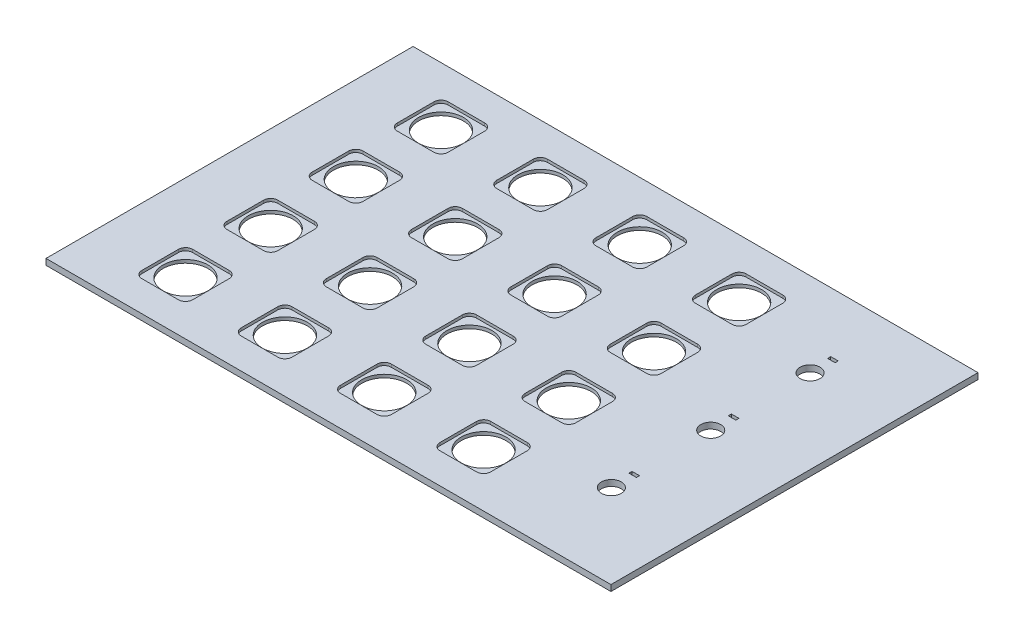
SolidWorks part; units mm, degrees
ref_plane "Front Plane" through (0, 0, 0) normal (0, 0, 1) x (1, 0, 0)
ref_plane "Top Plane" through (0, 0, 0) normal (0, 1, 0) x (1, 0, 0)
ref_plane "Right Plane" through (0, 0, 0) normal (1, 0, 0) x (0, 0, -1)
sketch "Sketch1" plane through (0, 0, 0) normal (0, 1, 0) x (1, 0, 0)
  line L0 (-70, 86.9805) -> (-70, -106.8016) construction
  line L1 (99.5, 64.65) -> (-99.5, 64.65)
  line L2 (99.5, 64.65) -> (99.5, -64.65)
  line L3 (99.5, -64.65) -> (-99.5, -64.65)
  line L4 (-99.5, 64.65) -> (-99.5, -64.65)
  line L5 (99.5, 64.65) -> (-99.5, -64.65) construction
  line L6 (99.5, -64.65) -> (-99.5, 64.65) construction
  line L7 (0, 64.65) -> (0, -64.65) construction
  line L8 (-99.5, 0) -> (99.5, 0) construction
  line L9 (-70, 45) -> (-35, 45) construction
  line L10 (60.6732, 35) -> (77.1303, 35) construction
  line L11 (68.675, 43.6) -> (71.325, 43.6)
  line L12 (68.675, 43.6) -> (68.675, 42.5)
  line L13 (68.675, 42.5) -> (71.325, 42.5)
  line L14 (71.325, 43.6) -> (71.325, 42.5)
  line L15 (68.675, 43.6) -> (71.325, 42.5) construction
  line L16 (68.675, 42.5) -> (71.325, 43.6) construction
  line L17 (68.675, 8.6) -> (68.675, 7.5)
  line L18 (68.675, 8.6) -> (71.325, 8.6)
  line L19 (71.325, 8.6) -> (71.325, 7.5)
  line L20 (68.675, 7.5) -> (71.325, 7.5)
  line L21 (68.675, -26.4) -> (68.675, -27.5)
  line L22 (68.675, -26.4) -> (71.325, -26.4)
  line L23 (71.325, -26.4) -> (71.325, -27.5)
  line L24 (68.675, -27.5) -> (71.325, -27.5)
  circle A0 centre (-70, 45) radius 7.9
  circle A1 centre (-35, 45) radius 7.9
  circle A2 centre (0, 45) radius 7.9
  circle A3 centre (35, 45) radius 7.9
  circle A4 centre (-35, 15) radius 7.9
  circle A5 centre (0, 15) radius 7.9
  circle A6 centre (35, 15) radius 7.9
  circle A7 centre (-35, -15) radius 7.9
  circle A8 centre (0, -15) radius 7.9
  circle A9 centre (35, -15) radius 7.9
  circle A10 centre (-35, -45) radius 7.9
  circle A11 centre (0, -45) radius 7.9
  circle A12 centre (35, -45) radius 7.9
  circle A13 centre (-70, 15) radius 7.9
  circle A14 centre (-70, -15) radius 7.9
  circle A15 centre (-70, -45) radius 7.9
  circle A16 centre (70, 35) radius 3.5
  circle A17 centre (70, 0) radius 3.5
  circle A18 centre (70, -35) radius 3.5
  point P0 (0, 0)
  point P14 (70, 43.05)
  dimension "D3" = 15.8
  dimension "D15" = 7
  dimension "D19" = 3
  dimension "D1" = 129.3
  dimension "D2" = 199
  dimension "D4" = 4
  dimension "D6" = 35
  dimension "D7" = 19.65
  dimension "D8" = 19.65
  dimension "D9" = 3
  dimension "D10" = 29.65
  dimension "D11" = 29.65
  dimension "D12" = 35
  dimension "D13" = 29.5
  dimension "D14" = 29.5
  dimension "D16" = 2.65
  dimension "D17" = 7.5
  dimension "D18" = 1.1
  dimension "D20" = 7.5
  dimension "D5" = 4
extrude "Boss-Extrude1" add sketch "Sketch1" along normal blind 2.13
sketch "Sketch2" plane through (0, 2.13, 0) normal (0, 1, 0) x (1, 0, 0)
  line L0 (-78.95, 53.95) -> (-61.05, 36.05) construction
  line L1 (-78.95, 53.95) -> (-61.05, 53.95)
  line L2 (-78.95, 53.95) -> (-78.95, 36.05)
  line L3 (-78.95, 36.05) -> (-61.05, 36.05)
  line L4 (-61.05, 53.95) -> (-61.05, 36.05)
  line L5 (-43.95, 36.05) -> (-26.05, 36.05)
  line L6 (-43.95, 53.95) -> (-26.05, 53.95)
  line L7 (-26.05, 53.95) -> (-26.05, 36.05)
  line L8 (-43.95, 53.95) -> (-43.95, 36.05)
  line L9 (-8.95, 36.05) -> (8.95, 36.05)
  line L10 (-8.95, 53.95) -> (8.95, 53.95)
  line L11 (8.95, 53.95) -> (8.95, 36.05)
  line L12 (-8.95, 53.95) -> (-8.95, 36.05)
  line L13 (26.05, 36.05) -> (43.95, 36.05)
  line L14 (26.05, 53.95) -> (43.95, 53.95)
  line L15 (43.95, 53.95) -> (43.95, 36.05)
  line L16 (26.05, 53.95) -> (26.05, 36.05)
  line L17 (-43.95, 6.05) -> (-26.05, 6.05)
  line L18 (-43.95, 23.95) -> (-26.05, 23.95)
  line L19 (-26.05, 23.95) -> (-26.05, 6.05)
  line L20 (-43.95, 23.95) -> (-43.95, 6.05)
  line L21 (-8.95, 6.05) -> (8.95, 6.05)
  line L22 (-8.95, 23.95) -> (8.95, 23.95)
  line L23 (8.95, 23.95) -> (8.95, 6.05)
  line L24 (-8.95, 23.95) -> (-8.95, 6.05)
  line L25 (26.05, 6.05) -> (43.95, 6.05)
  line L26 (26.05, 23.95) -> (43.95, 23.95)
  line L27 (43.95, 23.95) -> (43.95, 6.05)
  line L28 (26.05, 23.95) -> (26.05, 6.05)
  line L29 (-43.95, -23.95) -> (-26.05, -23.95)
  line L30 (-43.95, -6.05) -> (-26.05, -6.05)
  line L31 (-26.05, -6.05) -> (-26.05, -23.95)
  line L32 (-43.95, -6.05) -> (-43.95, -23.95)
  line L33 (-8.95, -23.95) -> (8.95, -23.95)
  line L34 (-8.95, -6.05) -> (8.95, -6.05)
  line L35 (8.95, -6.05) -> (8.95, -23.95)
  line L36 (-8.95, -6.05) -> (-8.95, -23.95)
  line L37 (26.05, -23.95) -> (43.95, -23.95)
  line L38 (26.05, -6.05) -> (43.95, -6.05)
  line L39 (43.95, -6.05) -> (43.95, -23.95)
  line L40 (26.05, -6.05) -> (26.05, -23.95)
  line L41 (-43.95, -53.95) -> (-26.05, -53.95)
  line L42 (-43.95, -36.05) -> (-26.05, -36.05)
  line L43 (-26.05, -36.05) -> (-26.05, -53.95)
  line L44 (-43.95, -36.05) -> (-43.95, -53.95)
  line L45 (-8.95, -53.95) -> (8.95, -53.95)
  line L46 (-8.95, -36.05) -> (8.95, -36.05)
  line L47 (8.95, -36.05) -> (8.95, -53.95)
  line L48 (-8.95, -36.05) -> (-8.95, -53.95)
  line L49 (26.05, -53.95) -> (43.95, -53.95)
  line L50 (26.05, -36.05) -> (43.95, -36.05)
  line L51 (43.95, -36.05) -> (43.95, -53.95)
  line L52 (26.05, -36.05) -> (26.05, -53.95)
  line L53 (-78.95, 6.05) -> (-61.05, 6.05)
  line L54 (-78.95, 23.95) -> (-61.05, 23.95)
  line L55 (-61.05, 23.95) -> (-61.05, 6.05)
  line L56 (-78.95, 23.95) -> (-78.95, 6.05)
  line L57 (-78.95, -23.95) -> (-61.05, -23.95)
  line L58 (-78.95, -6.05) -> (-61.05, -6.05)
  line L59 (-61.05, -6.05) -> (-61.05, -23.95)
  line L60 (-78.95, -6.05) -> (-78.95, -23.95)
  line L61 (-78.95, -53.95) -> (-61.05, -53.95)
  line L62 (-78.95, -36.05) -> (-61.05, -36.05)
  line L63 (-61.05, -36.05) -> (-61.05, -53.95)
  line L64 (-78.95, -36.05) -> (-78.95, -53.95)
  circle A0 centre (-70, 45) radius 7.9 construction
  point P9 (-70, 45)
  dimension "D1" = 17.9
  dimension "D2" = 4
  dimension "D3" = 4
extrude "Cut-Extrude1" cut sketch "Sketch2" against normal blind 1
fillet "Fillet1" radius 2.5 64 edges at (-61.05, 1.63, -53.95) (-61.05, 1.63, -6.05) (-61.05, 1.63, -36.05) (-78.95, 1.63, -23.95) (-78.95, 1.63, -53.95) (-43.95, 1.63, -53.95) (-78.95, 1.63, -6.05) (-43.95, 1.63, -36.05) (-26.05, 1.63, -53.95) (-61.05, 1.63, -23.95) (8.95, 1.63, -53.95) (43.95, 1.63, -53.95) (43.95, 1.63, -23.95) (43.95, 1.63, 6.05) (43.95, 1.63, 36.05) (8.95, 1.63, 36.05) (8.95, 1.63, 6.05) (8.95, 1.63, -23.95) (-61.05, 1.63, 6.05) (-61.05, 1.63, 36.05) (-26.05, 1.63, 36.05) (-26.05, 1.63, 6.05) (-26.05, 1.63, -23.95) (-26.05, 1.63, 23.95) (-61.05, 1.63, 53.95) (-26.05, 1.63, 53.95) (8.95, 1.63, 53.95) (43.95, 1.63, 53.95) (-61.05, 1.63, 23.95) (8.95, 1.63, 23.95) (43.95, 1.63, 23.95) (43.95, 1.63, -36.05) (8.95, 1.63, -36.05) (-26.05, 1.63, -36.05) (-26.05, 1.63, -6.05) (8.95, 1.63, -6.05) (43.95, 1.63, -6.05) (-78.95, 1.63, 23.95) (-78.95, 1.63, 53.95) (-43.95, 1.63, 53.95) (-8.95, 1.63, 53.95) (26.05, 1.63, 53.95) (26.05, 1.63, 23.95) (26.05, 1.63, -6.05) (-43.95, 1.63, -6.05) (26.05, 1.63, -36.05) (-8.95, 1.63, -6.05) (-8.95, 1.63, -36.05) (-78.95, 1.63, -36.05) (-43.95, 1.63, 6.05) (-78.95, 1.63, 36.05) (-78.95, 1.63, 6.05) (-43.95, 1.63, 36.05) (-8.95, 1.63, 36.05) (-8.95, 1.63, 6.05) (-43.95, 1.63, -23.95) (-8.95, 1.63, -23.95) (-8.95, 1.63, -53.95) (26.05, 1.63, -53.95) (26.05, 1.63, -23.95) (26.05, 1.63, 6.05) (26.05, 1.63, 36.05) (-43.95, 1.63, 23.95) (-8.95, 1.63, 23.95)
